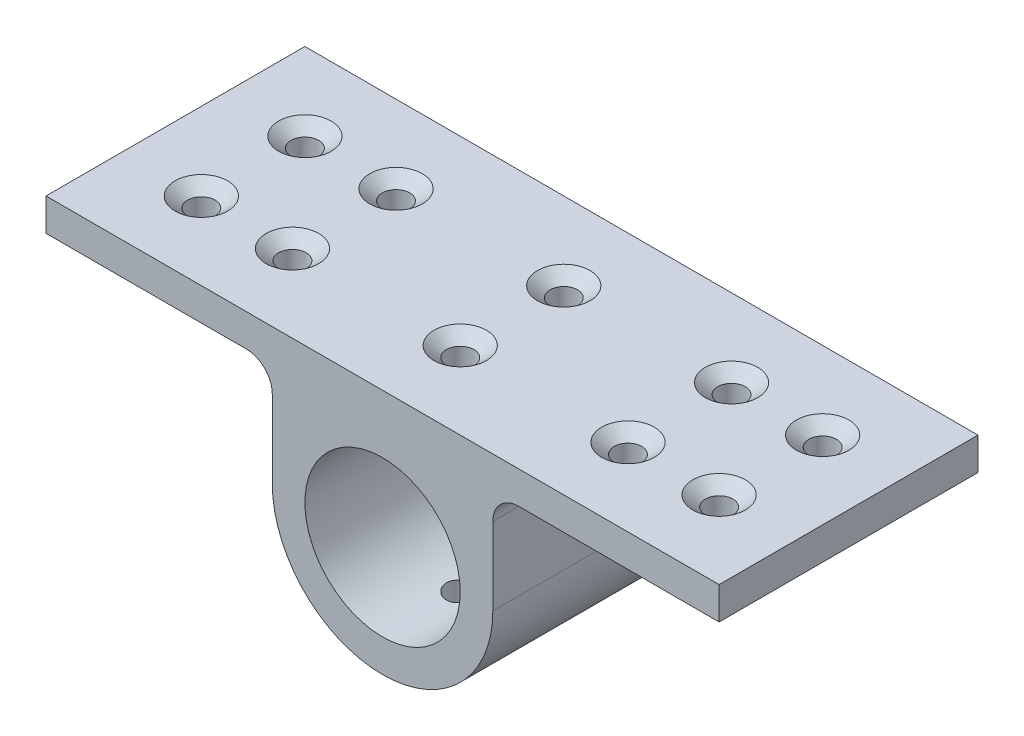
SolidWorks part; units mm, degrees
material "1060 Alloy"
ref_plane "Front" through (0, 0, 0) normal (0, 0, 1) x (1, 0, 0)
ref_plane "Top" through (0, 0, 0) normal (0, 1, 0) x (1, 0, 0)
ref_plane "Right" through (0, 0, 0) normal (1, 0, 0) x (0, 0, -1)
sketch "Sketch2" plane through (0, 0, 0) normal (0, 0, 1) x (1, 0, 0)
  line L0 (0, 44.6371) -> (0, -49.6431) construction
  line L1 (-86.1037, 0) -> (93.6127, 0) construction
  line L2 (82.55, 0) -> (-82.55, 0)
  line L3 (-82.55, 0) -> (-82.55, -7.9502)
  line L4 (-82.55, -7.9502) -> (-33.401, -7.9502)
  line L5 (82.55, -7.9502) -> (33.401, -7.9502)
  line L6 (82.55, 0) -> (82.55, -7.9502)
  line L7 (-27.051, -14.3002) -> (-27.051, -33.3502)
  line L8 (27.051, -14.3002) -> (27.051, -33.3502)
  arc A0 (-33.401, -7.9502) -> (-27.051, -14.3002) centre (-33.401, -14.3002) cw
  arc A1 (-27.051, -33.3502) -> (27.051, -33.3502) centre (0, -33.3502) ccw
  arc A2 (33.401, -7.9502) -> (27.051, -14.3002) centre (33.401, -14.3002) ccw
  point P17 (0, 0)
  dimension "D3" = 6.35
  dimension "D4" = 33.3502
  dimension "D5" = 27.051
  dimension "D1" = 165.1
  dimension "D2" = 7.9502
extrude "Boss-Extrude1" add sketch "Sketch2" along normal mid plane 63.5
sketch "Sketch3" plane through (0, 0, 31.75) normal (0, 0, 1) x (1, 0, 0)
  circle A0 centre (0, -33.3502) radius 19.05
  dimension "D1" = 38.1
extrude "Cut-Extrude1" cut sketch "Sketch3" against normal through all
sketch "Sketch6" plane through (0, 0, 0) normal (0, 1, 0) x (1, 0, 0)
  line L0 (0, 38.2684) -> (0, -51.3939) construction
  line L1 (-92.3896, 0) -> (99.8899, 0) construction
hole_wizard "CSK for 1/4 Flat Head Machine Screw (100)2" positions "Sketch9" profile "Sketch10" countersink size "1/4" standard "ANSI Inch" end condition through all
sketch "Sketch9" plane through (0, 0, 0) normal (0, 1, 0) x (1, 0, 0)
  line L0 (0, 38.2684) -> (0, -51.3939) construction
  line L1 (82.55, -31.75) -> (-82.55, -31.75) construction
  line L2 (82.55, -31.75) -> (82.55, 31.75) construction
  line L3 (-82.55, -31.75) -> (-82.55, 31.75) construction
  line L4 (82.55, 31.75) -> (-82.55, 31.75) construction
  point P0 (0, -12.7)
  point P4 (41.148, -12.7)
  point P6 (63.5, -12.7)
  point P8 (-41.148, -12.7)
  point P10 (-63.5, -12.7)
  point P23 (-41.148, 12.7)
  point P25 (-63.5, 12.7)
  point P27 (0, 12.7)
  point P29 (41.148, 12.7)
  point P31 (63.5, 12.7)
  dimension "D1" = 19.05
  dimension "D2" = 19.05
  dimension "D3" = 22.352
  dimension "D4" = 19.05
  dimension "D5" = 22.352
  dimension "D6" = 19.05
sketch "Sketch10" plane through (0, 0, 12.7) normal (1, 0, 0) x (0, 0, 1)
  line L0 (0, 0) -> (0, 60.4012)
  line L1 (0, 60.4012) -> (3.3782, 60.4012)
  line L2 (3.3782, 60.4012) -> (3.3782, 2.5682)
  line L3 (3.3782, 2.5682) -> (6.4389, 0)
  line L5 (6.4389, 0) -> (0, 0)
  line L6 (-3.3782, 2.5682) -> (-6.4389, 0) construction
  line L11 (0, -6.35) -> (0, 107.95) construction
  dimension "Thru Hole Dia." = 6.7564
  dimension "Thru Hole Depth" = 60.4012
  dimension "Near C'Sink Dia." = 12.8778
  dimension "Near C'Sink Angle" = 100
